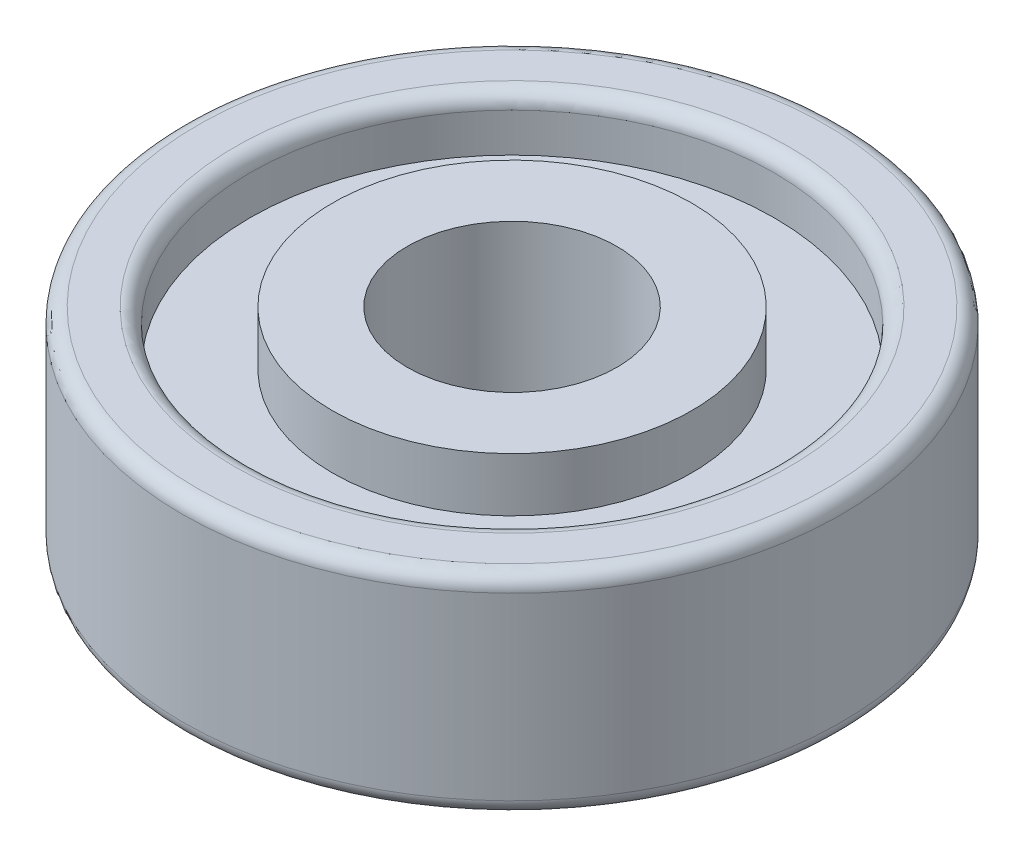
SolidWorks part; units mm, degrees
material "Plain Carbon Steel"
ref_plane "Front Plane" through (0, 0, 0) normal (0, 0, 1) x (1, 0, 0)
ref_plane "Top Plane" through (0, 0, 0) normal (0, 1, 0) x (1, 0, 0)
ref_plane "Right Plane" through (0, 0, 0) normal (1, 0, 0) x (0, 0, -1)
sketch "Sketch1" plane through (0, 0, 0) normal (0, 1, 0) x (1, 0, 0)
  circle A0 centre (0, 0) radius 11
  dimension "D1" = 22
extrude "Boss-Extrude1" add sketch "Sketch1" along normal mid plane 7
sketch "Sketch2" plane through (0, 3.5, 0) normal (0, 1, 0) x (1, 0, 0)
  circle A0 centre (0, 0) radius 8.75
  circle A1 centre (0, 0) radius 3.5
  circle A2 centre (0, 0) radius 6
  dimension "D1" = 7
  dimension "D2" = 17.5
  dimension "D3" = 2.5
extrude "Cut-Extrude2" cut sketch "Sketch2" against normal through all contours A1
sketch "Sketch3" plane through (0, 3.5, 0) normal (0, 1, 0) x (1, 0, 0)
  circle A0 centre (0, 0) radius 8.75
  circle A3 centre (0, 0) radius 6
  circle A4 centre (0, 0) radius 6
  dimension "D1" = 17.5
  dimension "D2" = 2.5
extrude "Cut-Extrude4" cut sketch "Sketch3" against normal blind 1.8 contours A0 | A4
mirror "Mirror1" about plane through (0, 0, 0) normal (0, 1, 0) of "Cut-Extrude4"
fillet "Fillet1" radius 0.5 4 edges at (0, -3.5, 8.75) (0, -3.5, 11) (0, 3.5, 8.75) (0, 3.5, 11)
